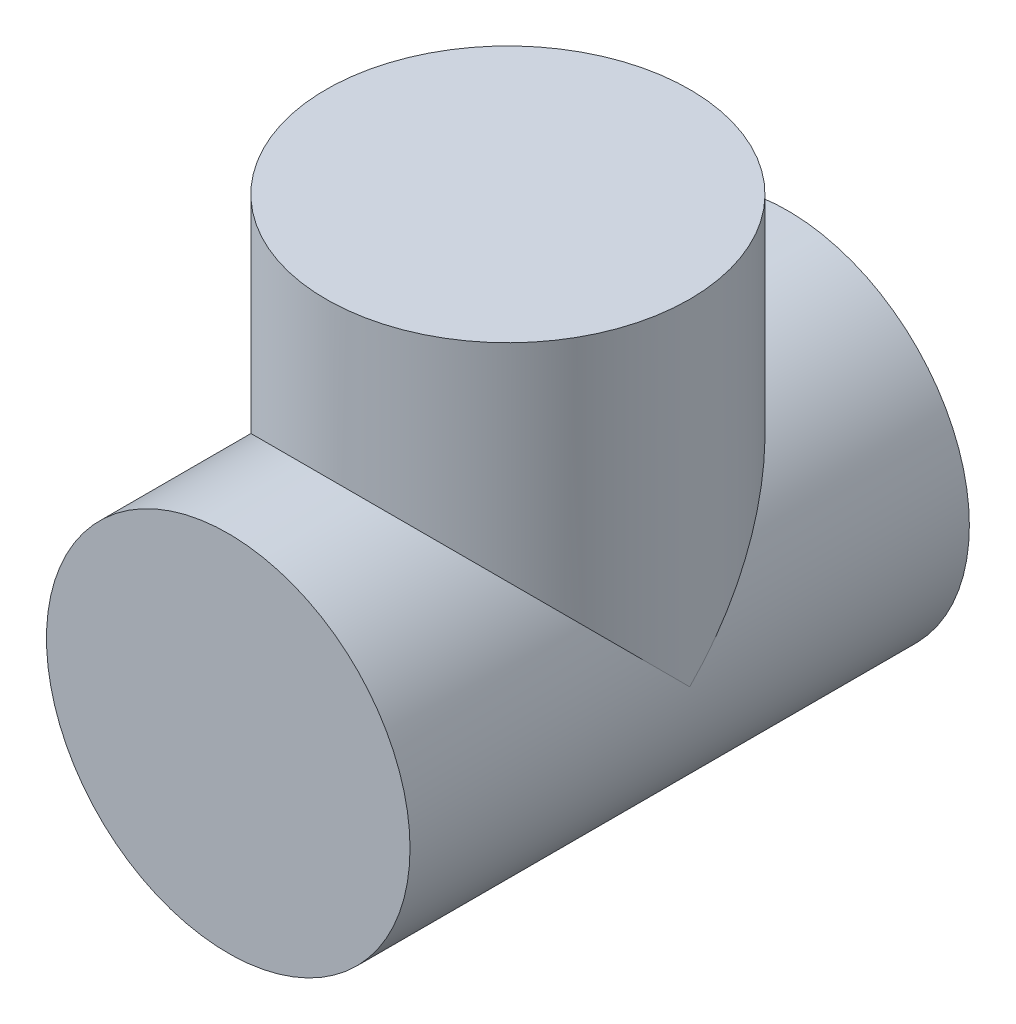
SolidWorks part; units mm, degrees
ref_plane "Front Plane" through (0, 0, 0) normal (0, 0, 1) x (1, 0, 0)
ref_plane "Top Plane" through (0, 0, 0) normal (0, 1, 0) x (1, 0, 0)
ref_plane "Right Plane" through (0, 0, 0) normal (1, 0, 0) x (0, 0, -1)
sketch "Sketch1" plane through (0, 0, 0) normal (1, 0, 0) x (0, 0, -1)
  line L0 (-50, 0) -> (50, 0)
  line L1 (50, 0) -> (50, 120)
  dimension "D1" = 100
  dimension "D2" = 120
ref_plane "Plane1" through (0, 0, 50) normal (0, 0, 1) x (1, 0, 0)
sketch "Sketch2" plane through (0, 0, 50) normal (0, 0, 1) x (1, 0, 0)
  circle A0 centre (0, 0) radius 65
  dimension "D1" = 130
sweep "Sweep1" add profiles "Sketch2" path "Sketch1"
ref_plane "Plane2" through (0, 0, -50) normal (0, 0, 1) x (1, 0, 0)
mirror "Mirror1" about plane through (0, 0, -50) normal (0, 0, 1) of "Sweep1"
